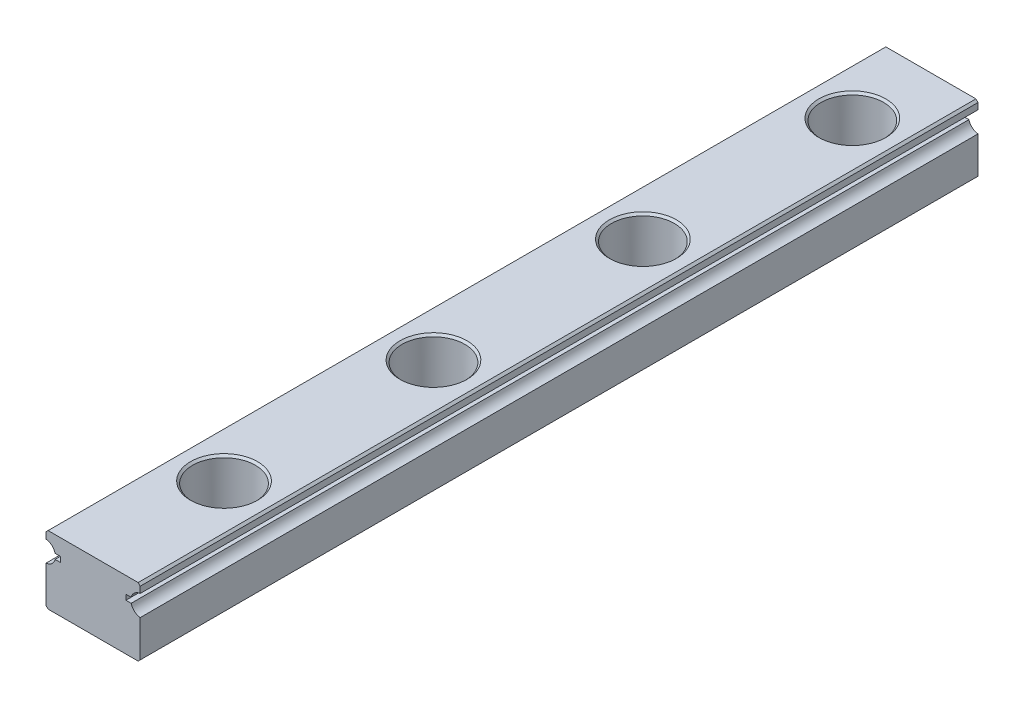
SolidWorks part; units mm, degrees
material "AISI 1035 鋼 (SS)"
ref_plane "Спереди" through (0, 0, 0) normal (0, 0, 1) x (1, 0, 0)
ref_plane "Сверху" through (0, 0, 0) normal (0, 1, 0) x (1, 0, 0)
ref_plane "Справа" through (0, 0, 0) normal (1, 0, 0) x (0, 0, -1)
sketch "Sketch1" plane through (0, 0, 0) normal (0, 0, 1) x (1, 0, 0)
  line L0 (0, 0) -> (0, 4.3706) construction
  line L1 (-4.3, -3.25) -> (4.3, -3.25)
  line L2 (-4.5, -3.05) -> (-4.5, 0.455)
  line L3 (-4.3, 3.25) -> (4.3, 3.25)
  line L4 (4.5, -3.05) -> (4.5, 0.455)
  line L5 (-4.5, -3.25) -> (4.5, 3.25) construction
  line L6 (-4.5, 3.25) -> (4.5, -3.25) construction
  line L7 (-4.5, 2.445) -> (-4.5, 3.05)
  line L8 (4.5, 2.445) -> (4.5, 3.05)
  line L9 (-4.5, -3.05) -> (-4.3, -3.25)
  line L10 (4.3, -3.25) -> (4.5, -3.05)
  line L11 (4.3, 3.25) -> (4.5, 3.05)
  line L12 (-4.5, 3.05) -> (-4.3, 3.25)
  line L13 (3.6318, 1.2) -> (3.1318, 1.2)
  line L14 (-3.6318, 1.2) -> (-3.1318, 1.2)
  line L15 (3.1318, 1.2) -> (3.1318, 1.7)
  line L16 (-3.6318, 1.7) -> (-3.1318, 1.7)
  line L17 (-3.1318, 1.2) -> (-3.1318, 1.7)
  line L18 (3.6318, 1.7) -> (3.1318, 1.7)
  arc A0 (-4.5, 2.445) -> (-3.6318, 1.7) centre (-4.6, 1.45) cw
  arc A1 (4.5, 2.445) -> (3.6318, 1.7) centre (4.6, 1.45) ccw
  arc A2 (-3.6318, 1.2) -> (-4.5, 0.455) centre (-4.6, 1.45) cw
  arc A3 (3.6318, 1.2) -> (4.5, 0.455) centre (4.6, 1.45) ccw
  point P0 (0, 0)
  dimension "D4" = 1
  dimension "D5" = 0.1
  dimension "D1" = 9
  dimension "D2" = 6.5
  dimension "D3" = 1.8
  dimension "D6" = 0.5
  dimension "D7" = 0.5
extrude "Extrude1" add sketch "Sketch1" along normal blind 80
hole_wizard "M3 平盤頭機械螺釘的柱孔1" positions "草圖1" profile "草圖2" counterbore size "M3" standard "Ansi Metric" end condition through all
sketch "草圖1" plane through (0, 3.25, 0) normal (0, 1, 0) x (1, 0, 0)
  line L0 (0, 0) -> (0, -7.5) construction
  line L1 (4.3, 0) -> (-4.3, 0) construction
  point P0 (0, -7.5)
  dimension "D1" = 7.5
sketch "草圖2" plane through (0, 3.25, 7.5) normal (1, 0, 0) x (0, 0, 1)
  line L0 (0, 0) -> (0, 6.5)
  line L1 (0, 6.5) -> (1.75, 6.5)
  line L3 (1.75, 6.5) -> (1.75, 4.5)
  line L4 (1.75, 4.5) -> (3, 4.5)
  line L5 (3, 4.5) -> (3, 0)
  line L7 (3, 0) -> (0, 0)
  line L11 (0, -6.35) -> (0, 107.95) construction
  dimension "砮 ふ 畖" = 3.5
  dimension "砮 ふ瞏 " = 6.5
  dimension "琖ふ 畖" = 6
  dimension "琖ふ瞏 " = 4.5
chamfer "導角1" distance 0.2 angle 45 2 edges at (0, -3.25, 9.25) (0, 3.25, 10.5)
pattern_linear "直線複製排列1" count 4 spacing 20 along (0, 0, 1) of "導角1", "M3 平盤頭機械螺釘的柱孔1"
